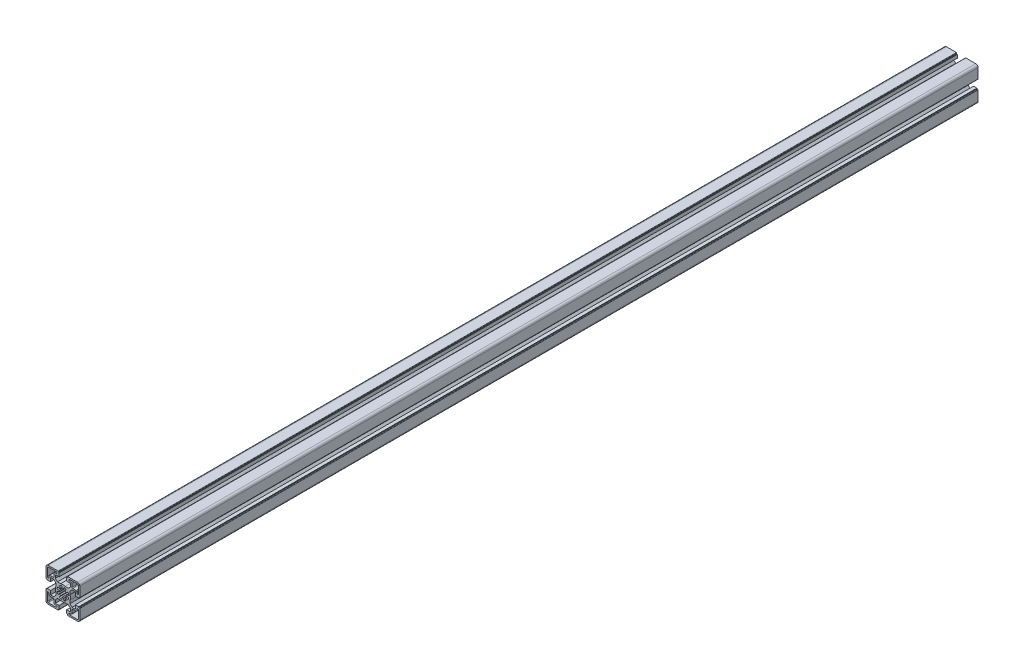
SolidWorks part; units mm, degrees
material "7079 Alloy"
ref_plane "Front Plane" through (0, 0, 0) normal (0, 0, 1) x (1, 0, 0)
ref_plane "Top Plane" through (0, 0, 0) normal (0, 1, 0) x (1, 0, 0)
ref_plane "Right Plane" through (0, 0, 0) normal (1, 0, 0) x (0, 0, -1)
sketch "Sketch1" plane through (0, 0, 0) normal (0, 0, 1) x (1, 0, 0)
  line L0 (0, 34.901) -> (0, -38.8683) construction
  line L1 (-27.7848, 0) -> (42.6814, 0) construction
  line L88 (0.8682, 4.924) -> (1.3892, 7.8784)
  line L89 (-0.8682, 4.924) -> (-1.3892, 7.8785)
  line L90 (-4.5886, 6.5532) -> (-2.8679, 4.0957)
  line L91 (-4.0957, 2.8679) -> (-6.5532, 4.5886)
  line L92 (-7.8784, 1.3892) -> (-4.924, 0.8682)
  line L93 (-7.8785, -1.3892) -> (-4.924, -0.8682)
  line L94 (-6.5532, -4.5886) -> (-4.0957, -2.8679)
  line L95 (-4.5886, -6.5532) -> (-2.8679, -4.0957)
  line L96 (-1.3892, -7.8784) -> (-0.8682, -4.924)
  line L97 (0.8682, -4.924) -> (1.3892, -7.8784)
  line L98 (4.5886, -6.5532) -> (2.8679, -4.0957)
  line L99 (4.0957, -2.8679) -> (6.5532, -4.5886)
  line L100 (7.8784, -1.3892) -> (4.924, -0.8682)
  line L101 (4.924, 0.8682) -> (7.8784, 1.3892)
  line L102 (4.0957, 2.8679) -> (6.5532, 4.5886)
  line L103 (2.8679, 4.0957) -> (4.5886, 6.5532)
  line L104 (-5, -16.4999) -> (-5, -20.9999)
  line L105 (-5, -20.9999) -> (-5.8, -20.9999)
  line L106 (-5.8, -20.9999) -> (-5.8, -22)
  line L107 (-6.3, -22.5) -> (-19.5, -22.5)
  line L108 (-22.5, -19.5) -> (-22.5, -6.2999)
  line L109 (-22, -5.7999) -> (-21, -5.7999)
  line L110 (-21, -5.7999) -> (-21, -4.9999)
  line L111 (-21, -4.9999) -> (-16.5, -4.9999)
  line L112 (-16.5, -4.9999) -> (-16.5, -10.0499)
  line L113 (-16.5, -10.0499) -> (-12.3429, -10.0499)
  line L114 (-12.3429, -10.0499) -> (-9.5, -7.207)
  line L115 (-9.5, -7.207) -> (-9.5, -3.1226)
  line L116 (-9.5, 3.1227) -> (-9.5, 7.207)
  line L117 (-9.5, 7.207) -> (-12.3429, 10.0499)
  line L118 (-12.3429, 10.0499) -> (-16.5, 10.0499)
  line L119 (-16.5, 10.0499) -> (-16.5, 4.9999)
  line L120 (-16.5, 4.9999) -> (-21, 4.9999)
  line L121 (-21, 4.9999) -> (-21, 5.7999)
  line L122 (-21, 5.7999) -> (-22, 5.7999)
  line L123 (-22.5, 6.2999) -> (-22.5, 19.5)
  line L124 (-19.5, 22.5) -> (-6.3, 22.5)
  line L125 (-5.7999, 21.9999) -> (-5.7999, 20.9999)
  line L126 (-5.7999, 20.9999) -> (-5, 20.9999)
  line L127 (-5, 20.9999) -> (-5, 16.5)
  line L128 (-5, 16.5) -> (-10.0501, 16.5)
  line L129 (-10.0501, 16.5) -> (-10.0501, 12.3428)
  line L130 (-10.0501, 12.3428) -> (-7.2072, 9.4999)
  line L131 (-7.2072, 9.4999) -> (-3.1228, 9.4999)
  line L132 (3.1226, 9.4999) -> (7.207, 9.4999)
  line L133 (7.207, 9.4999) -> (10.0499, 12.3428)
  line L134 (10.0499, 12.3428) -> (10.0499, 16.5)
  line L135 (10.0499, 16.5) -> (5, 16.5)
  line L136 (5, 16.5) -> (5, 21)
  line L137 (5, 21) -> (5.7999, 21)
  line L138 (5.7999, 21) -> (5.7999, 21.9999)
  line L139 (6.3, 22.5) -> (19.5001, 22.5)
  line L140 (22.5001, 6.2999) -> (22.5001, 19.5)
  line L141 (22.0001, 5.7999) -> (21, 5.7999)
  line L142 (21, 5.7999) -> (21, 4.9999)
  line L143 (21, 4.9999) -> (16.5, 4.9999)
  line L144 (16.5, 4.9999) -> (16.5, 10.0499)
  line L145 (16.5, 10.0499) -> (12.3429, 10.0499)
  line L146 (12.3429, 10.0499) -> (9.4999, 7.207)
  line L147 (9.4999, 7.207) -> (9.4999, 3.1227)
  line L148 (9.4999, -3.1226) -> (9.4999, -7.207)
  line L149 (9.4999, -7.207) -> (12.3429, -10.0499)
  line L150 (12.3429, -10.0499) -> (16.5, -10.0499)
  line L151 (16.5, -10.0499) -> (16.5, -4.9999)
  line L152 (16.5, -4.9999) -> (21, -4.9999)
  line L153 (21, -4.9999) -> (21, -5.7999)
  line L154 (21, -5.7999) -> (22.0001, -5.7999)
  line L155 (22.5001, -6.2999) -> (22.5001, -19.5)
  line L156 (6.3, -22.5) -> (19.5001, -22.5)
  line L157 (5.8, -22) -> (5.8, -20.9999)
  line L158 (5.8, -20.9999) -> (5, -20.9999)
  line L159 (5, -20.9999) -> (5, -16.4999)
  line L160 (5, -16.4999) -> (10.0499, -16.4999)
  line L161 (10.0499, -16.4999) -> (10.0499, -12.3428)
  line L162 (10.0499, -12.3428) -> (7.2069, -9.4998)
  line L163 (7.2069, -9.4998) -> (3.1226, -9.4998)
  line L164 (-3.1228, -9.4998) -> (-7.2071, -9.4998)
  line L165 (-7.2071, -9.4998) -> (-10.0501, -12.3428)
  line L166 (-10.0501, -12.3428) -> (-10.0501, -16.4999)
  line L167 (-10.0501, -16.4999) -> (-5, -16.4999)
  line L168 (-17.5001, -12) -> (-13.0001, -12)
  line L169 (-12.0001, -17.4999) -> (-12.0001, -13)
  line L170 (-11.0001, -18.4999) -> (-9.0001, -18.4999)
  line L171 (-19.5001, -20.5) -> (-9.0001, -20.5)
  line L172 (-20.5001, -19.5) -> (-20.5001, -8.9999)
  line L173 (-18.5001, -11) -> (-18.5001, -8.9999)
  line L174 (13, -12) -> (17.5, -12)
  line L175 (12, -17.4999) -> (12, -13)
  line L176 (9, -18.4999) -> (11, -18.4999)
  line L177 (9, -20.5) -> (19.5, -20.5)
  line L178 (20.5, -19.5) -> (20.5, -9.0001)
  line L179 (18.5, -11) -> (18.5, -9.0001)
  line L180 (-17.5001, 12) -> (-13.0001, 12)
  line L181 (-12.0001, 13) -> (-12.0001, 17.4999)
  line L182 (-11.0001, 18.4999) -> (-9.0001, 18.4999)
  line L183 (-19.5001, 20.5) -> (-9.0001, 20.5)
  line L184 (-20.5001, 8.9999) -> (-20.5001, 19.5)
  line L185 (-18.5001, 8.9999) -> (-18.5001, 11)
  line L186 (13, 12) -> (17.5, 12)
  line L187 (12, 13) -> (12, 17.4999)
  line L188 (9, 18.4999) -> (11, 18.4999)
  line L189 (9, 20.5) -> (19.5, 20.5)
  line L190 (20.5, 9.0001) -> (20.5, 19.5)
  line L191 (18.5, 9.0001) -> (18.5, 11)
  arc A56 (0.8682, 4.924) -> (-0.8682, 4.924) centre (0, 0) ccw
  arc A57 (-1.3892, 7.8785) -> (-4.5886, 6.5532) centre (0, 0) ccw
  arc A58 (-2.8679, 4.0957) -> (-4.0957, 2.8679) centre (0, 0) ccw
  arc A59 (-6.5532, 4.5886) -> (-7.8784, 1.3892) centre (0, 0) ccw
  arc A60 (-4.924, 0.8682) -> (-4.924, -0.8682) centre (0, 0) ccw
  arc A61 (-7.8785, -1.3892) -> (-6.5532, -4.5886) centre (0, 0) ccw
  arc A62 (-4.0957, -2.8679) -> (-2.8679, -4.0957) centre (0, 0) ccw
  arc A63 (-4.5886, -6.5532) -> (-1.3892, -7.8784) centre (0, 0) ccw
  arc A64 (-0.8682, -4.924) -> (0.8682, -4.924) centre (0, 0) ccw
  arc A65 (1.3892, -7.8784) -> (4.5886, -6.5532) centre (0, 0) ccw
  arc A66 (2.8679, -4.0957) -> (4.0957, -2.8679) centre (0, 0) ccw
  arc A67 (6.5532, -4.5886) -> (7.8784, -1.3892) centre (0, 0) ccw
  arc A68 (4.924, -0.8682) -> (4.924, 0.8682) centre (0, 0) ccw
  arc A69 (7.8784, 1.3892) -> (6.5532, 4.5886) centre (0, 0) ccw
  arc A70 (4.0957, 2.8679) -> (2.8679, 4.0957) centre (0, 0) ccw
  arc A71 (4.5886, 6.5532) -> (1.3892, 7.8784) centre (0, 0) ccw
  arc A72 (-6.3, -22.5) -> (-5.8, -22) centre (-6.3, -22) ccw
  arc A73 (-22.5, -19.5) -> (-19.5, -22.5) centre (-19.5, -19.5) ccw
  arc A74 (-22, -5.7999) -> (-22.5, -6.2999) centre (-22, -6.2999) ccw
  arc A75 (-9.5, 3.1227) -> (-9.5, -3.1226) centre (0, 0.0001) ccw
  arc A76 (-22.5, 6.2999) -> (-22, 5.7999) centre (-22, 6.2999) ccw
  arc A77 (-19.5, 22.5) -> (-22.5, 19.5) centre (-19.5, 19.5) ccw
  arc A78 (-5.7999, 21.9999) -> (-6.3, 22.5) centre (-6.3, 21.9999) ccw
  arc A79 (3.1226, 9.4999) -> (-3.1228, 9.4999) centre (-0.0001, -0.0001) ccw
  arc A80 (6.3, 22.5) -> (5.7999, 21.9999) centre (6.3, 21.9999) ccw
  arc A81 (22.5001, 19.5) -> (19.5001, 22.5) centre (19.5001, 19.5) ccw
  arc A82 (22.0001, 5.7999) -> (22.5001, 6.2999) centre (22.0001, 6.2999) ccw
  arc A83 (9.4999, -3.1226) -> (9.4999, 3.1227) centre (0, 0.0001) ccw
  arc A84 (22.5001, -6.2999) -> (22.0001, -5.7999) centre (22.0001, -6.2999) ccw
  arc A85 (19.5001, -22.5) -> (22.5001, -19.5) centre (19.5001, -19.5) ccw
  arc A86 (5.8, -22) -> (6.3, -22.5) centre (6.3, -22) ccw
  arc A87 (-3.1228, -9.4998) -> (3.1226, -9.4998) centre (-0.0001, 0.0001) ccw
  arc A88 (-18.5001, -11) -> (-17.5001, -12) centre (-17.5001, -11) ccw
  arc A89 (-12.0001, -13) -> (-13.0001, -12) centre (-13.0001, -13) ccw
  arc A90 (-12.0001, -17.4999) -> (-11.0001, -18.4999) centre (-11.0001, -17.4999) ccw
  arc A91 (-9.0001, -20.5) -> (-9.0001, -18.4999) centre (-9.0001, -19.5) ccw
  arc A92 (-20.5001, -19.5) -> (-19.5001, -20.5) centre (-19.5001, -19.5) ccw
  arc A93 (-18.5001, -8.9999) -> (-20.5001, -8.9999) centre (-19.5001, -8.9999) ccw
  arc A94 (17.5, -12) -> (18.5, -11) centre (17.5, -11) ccw
  arc A95 (13, -12) -> (12, -13) centre (13, -13) ccw
  arc A96 (11, -18.4999) -> (12, -17.4999) centre (11, -17.4999) ccw
  arc A97 (9, -18.4999) -> (9, -20.5) centre (9, -19.5) ccw
  arc A98 (19.5, -20.5) -> (20.5, -19.5) centre (19.5, -19.5) ccw
  arc A99 (20.5, -9.0001) -> (18.5, -9.0001) centre (19.5, -9.0001) ccw
  arc A100 (-17.5001, 12) -> (-18.5001, 11) centre (-17.5001, 11) ccw
  arc A101 (-13.0001, 12) -> (-12.0001, 13) centre (-13.0001, 13) ccw
  arc A102 (-11.0001, 18.4999) -> (-12.0001, 17.4999) centre (-11.0001, 17.4999) ccw
  arc A103 (-9.0001, 18.4999) -> (-9.0001, 20.5) centre (-9.0001, 19.5) ccw
  arc A104 (-19.5001, 20.5) -> (-20.5001, 19.5) centre (-19.5001, 19.5) ccw
  arc A105 (-20.5001, 8.9999) -> (-18.5001, 8.9999) centre (-19.5001, 8.9999) ccw
  arc A106 (18.5, 11) -> (17.5, 12) centre (17.5, 11) ccw
  arc A107 (12, 13) -> (13, 12) centre (13, 13) ccw
  arc A108 (12, 17.4999) -> (11, 18.4999) centre (11, 17.4999) ccw
  arc A109 (9, 20.5) -> (9, 18.4999) centre (9, 19.5) ccw
  arc A110 (20.5, 19.5) -> (19.5, 20.5) centre (19.5, 19.5) ccw
  arc A111 (18.5, 9.0001) -> (20.5, 9.0001) centre (19.5, 9.0001) ccw
  dimension "D5" = 10
  dimension "D1" = 45.0001
  dimension "D2" = 44.9999
  dimension "D3" = 12.5001
  dimension "D4" = 10
  dimension "D6" = 22.5001
extrude "Base-Extrude" add sketch "Sketch1" along normal blind 1196
